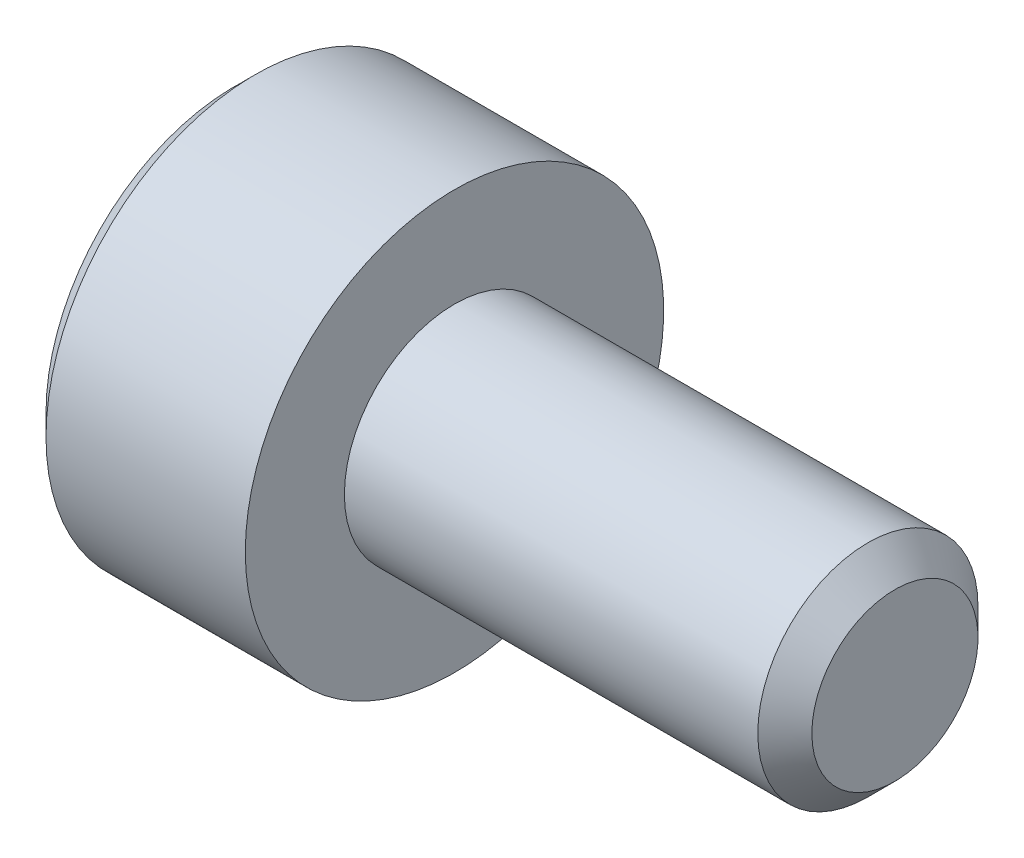
SolidWorks part; units mm, degrees
material "AISI 304"
ref_plane "正面" through (0, 0, 0) normal (0, 0, 1) x (1, 0, 0)
ref_plane "平面" through (0, 0, 0) normal (0, 1, 0) x (1, 0, 0)
ref_plane "右側面" through (0, 0, 0) normal (1, 0, 0) x (0, 0, -1)
ref_plane "Plane1" through (0, 0, 0) normal (0, 0, 1) x (1, 0, 0)
sketch "Sketch1" plane through (0, 0, 0) normal (0, 0, 1) x (1, 0, 0)
  line L0 (-2, 0) -> (-2, 1.71)
  line L1 (-2, 1.71) -> (-1.81, 1.9)
  line L2 (-1.81, 1.9) -> (0, 1.9)
  line L3 (0, 1.9) -> (0, 1)
  line L4 (0, 1) -> (3.7545, 1)
  line L5 (3.7545, 1) -> (4, 0.7545)
  line L6 (4, 0.7545) -> (4, 0)
  line L7 (4, 0) -> (-2, 0)
  line L8 (4, 0) -> (-2, 0) construction
  dimension "D1" = 1
revolve "Revolve1" add sketch "Sketch1" angle 360 about L8
cosmetic thread "Cosmetic Thread1"
ref_plane "Plane2" through (-2, 0, 0) normal (1, 0, 0) x (0, 0, -1)
sketch "Sketch2" plane through (-2, 0, 0) normal (1, 0, 0) x (0, 0, -1)
  line L0 (-0.75, -0.433) -> (0, -0.866)
  line L1 (0, -0.866) -> (0.75, -0.433)
  line L2 (0.75, -0.433) -> (0.75, 0.433)
  line L3 (0.75, 0.433) -> (0, 0.866)
  line L4 (0, 0.866) -> (-0.75, 0.433)
  line L5 (-0.75, 0.433) -> (-0.75, -0.433)
extrude "Cut-Extrude1" cut sketch "Sketch2" along normal blind 0.8
